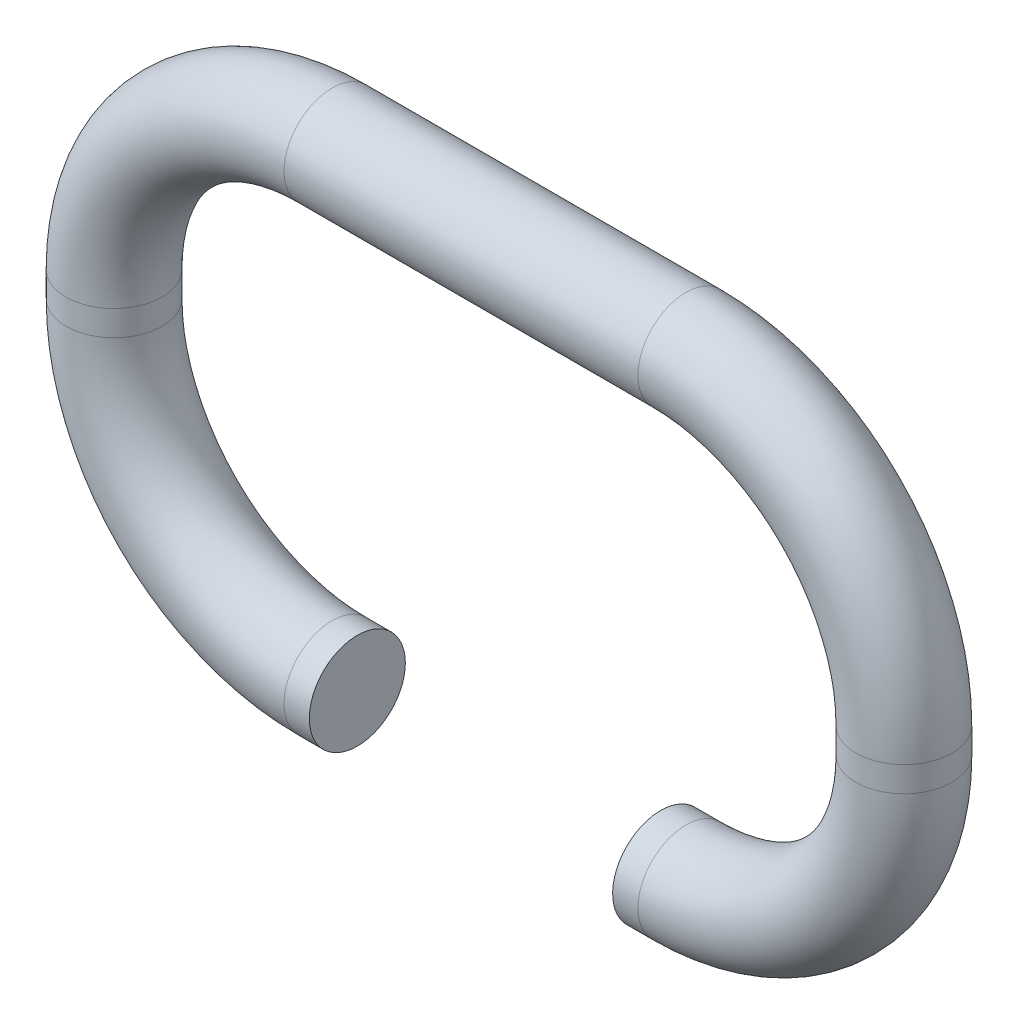
SolidWorks part; units mm, degrees
material "Plastique personnalisé"
ref_plane "Plan de face" through (0, 0, 0) normal (0, 0, 1) x (1, 0, 0)
ref_plane "Plan de dessus" through (0, 0, 0) normal (0, 1, 0) x (1, 0, 0)
ref_plane "Plan de droite" through (0, 0, 0) normal (1, 0, 0) x (0, 0, -1)
sketch "Esquisse23" plane through (0, 0, 0) normal (0, 0, 1) x (1, 0, 0)
  line L0 (1, -2) -> (15, -2)
  line L1 (16, -3) -> (16, -4)
  line L2 (0, -3) -> (0, -4)
  line L3 (1, -5) -> (2, -5)
  line L4 (15, -5) -> (14, -5)
  arc A0 (0, -3) -> (1, -2) centre (1, -3) cw
  arc A1 (16, -3) -> (15, -2) centre (15, -3) ccw
  arc A2 (16, -4) -> (15, -5) centre (15, -4) cw
  arc A3 (0, -4) -> (1, -5) centre (1, -4) ccw
  point P7 (0, -2)
  point P9 (16, 0)
  point P12 (0, 0)
  point P15 (16, -5)
  point P18 (0, -5)
  dimension "D5" = 1
  dimension "D6" = 1
  dimension "D1" = 16
  dimension "D2" = 5
  dimension "D3" = 2
  dimension "D4" = 2
  dimension "D7" = 2
ref_plane "Start" through (2, 0, 0) normal (1, 0, 0) x (0, 0, -1)
sketch "Esquisse25" plane through (2, 0, 0) normal (1, 0, 0) x (0, 0, -1)
  circle A0 centre (0, -12.6235) radius 1.9
  dimension "D1" = 3.8
sweep "Balayage7" add profiles "Esquisse25" path "Esquisse23"
